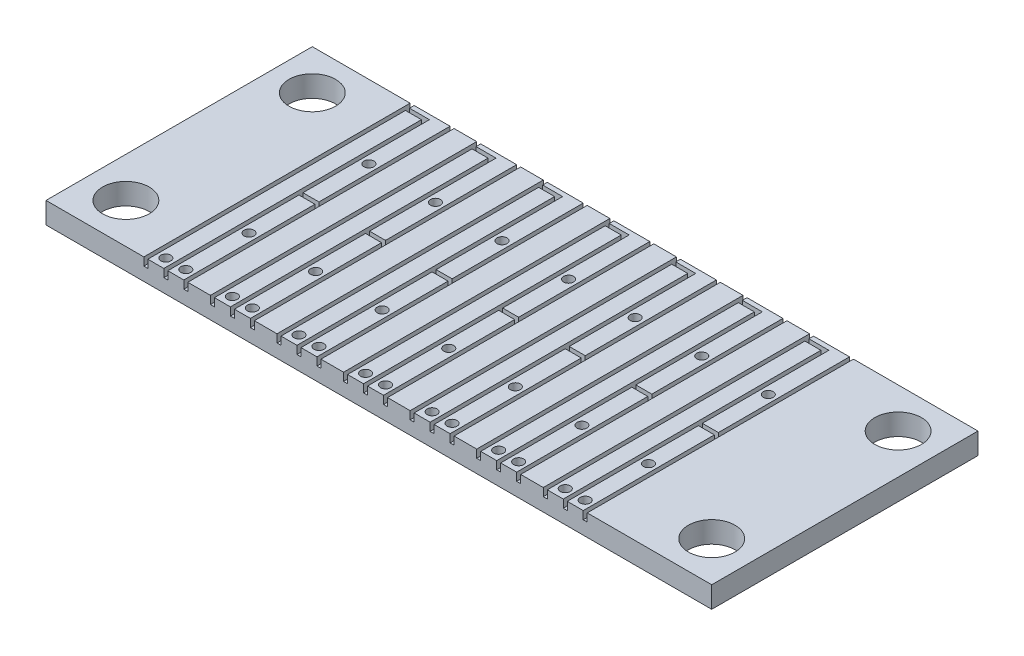
SolidWorks part; units mm, degrees
ref_plane "Front Plane" through (0, 0, 0) normal (0, 0, 1) x (1, 0, 0)
ref_plane "Top Plane" through (0, 0, 0) normal (0, 1, 0) x (1, 0, 0)
ref_plane "Right Plane" through (0, 0, 0) normal (1, 0, 0) x (0, 0, -1)
sketch "Sketch1" plane through (0, 0, 0) normal (0, 1, 0) x (1, 0, 0)
  line L1 (0, 0) -> (50, 0)
  line L2 (0, 0) -> (0, 20)
  line L3 (0, 20) -> (50, 20)
  line L4 (50, 0) -> (50, 20)
  circle A0 centre (3, 17) radius 1.75
  circle A1 centre (47, 3) radius 1.75
  circle A2 centre (3, 3) radius 1.75
  circle A3 centre (47, 17) radius 1.75
  dimension "D3" = 3.5
  dimension "D1" = 20
  dimension "D2" = 50
  dimension "D4" = 3
  dimension "D5" = 3
  dimension "D7" = 3
  dimension "D8" = 3
extrude "Boss-Extrude1" add sketch "Sketch1" along normal blind 1.6
sketch "Sketch2" plane through (0, 1.6, 0) normal (0, 1, 0) x (1, 0, 0)
  line L0 (50, 20) -> (0, 20) construction
  line L1 (7.5, 20) -> (10.5, 20)
  line L2 (7.5, 20) -> (7.5, 0)
  line L3 (7.5, 0) -> (10.5, 0)
  line L4 (10.5, 20) -> (10.5, 0)
  line L5 (0, 0) -> (50, 0) construction
  line L6 (0, 20) -> (0, 0) construction
  line L7 (9, 0) -> (9, 19.5)
  line L8 (9, 19.5) -> (7.5, 19.5)
  line L9 (10.5, 10) -> (9, 10)
  line L10 (9.15, 0) -> (9.15, 19.65)
  line L11 (9.15, 19.65) -> (7.5, 19.65)
  line L12 (8.85, 0) -> (8.85, 19.35)
  line L13 (8.85, 19.35) -> (7.5, 19.35)
  line L14 (7.35, 20) -> (7.35, 0)
  line L15 (7.65, 20) -> (7.65, 0)
  line L16 (10.35, 20) -> (10.35, 0)
  line L17 (10.65, 20) -> (10.65, 0)
  line L18 (10.5, 10.15) -> (9, 10.15)
  line L19 (10.5, 9.85) -> (9, 9.85)
  line L20 (7.35, 20) -> (7.65, 20)
  line L21 (10.35, 20) -> (10.65, 20)
  line L22 (7.5, 19.65) -> (7.5, 19.35)
  line L23 (9, 10.15) -> (9, 9.85)
  line L24 (10.5, 10.15) -> (10.5, 9.85)
  line L25 (7.35, 0) -> (7.65, 0)
  line L26 (8.85, 0) -> (9.15, 0)
  line L27 (10.35, 0) -> (10.65, 0)
  dimension "D1" = 7.5
  dimension "D2" = 3
  dimension "D3" = 0.5
  dimension "D4" = 0.15
  dimension "D5" = 0.15
  dimension "D6" = 0.15
  dimension "D7" = 0.15
  dimension "D8" = 0.15
  dimension "D9" = 0.15
  dimension "D10" = 0.15
  dimension "D11" = 0.15
sketch "Sketch3" plane through (0, 1.6, 0) normal (0, 1, 0) x (1, 0, 0)
  line L0 (7.5, 0) -> (10.5, 0) construction
  line L1 (10.5, 10) -> (9, 10) construction
  line L2 (9, 19.5) -> (7.5, 19.5) construction
  line L3 (9.75, 5.5) -> (9.75, 14.5) construction
  line L4 (8.25, 19.5) -> (8.25, 0.75) construction
  circle A0 centre (8.25, 0.75) radius 0.375
  circle A1 centre (9.75, 0.75) radius 0.375
  circle A2 centre (9.75, 5.5) radius 0.375
  circle A3 centre (9.75, 14.5) radius 0.375
  point P8 (8.25, 19.5)
  point P12 (9.75, 10)
  point P16 (9.75, 10)
  dimension "D1" = 0.75
  dimension "D3" = 9
  dimension "D2" = 0.75
extrude "Cut-Extrude1" cut sketch "Sketch3" against normal through all
extrude "Cut-Extrude2" cut sketch "Sketch2" against normal blind 0.6 contours L14 L25 L15 L20 | L12 L13 L22 L11 L10 L26 | L16 L27 L17 L21 | L19 L23 L18 L24
pattern_linear "LPattern1" count 7 spacing 5 along (1, 0, 0) of "Cut-Extrude1"
pattern_linear "LPattern2" count 7 spacing 5 along (1, 0, 0) of "Cut-Extrude2"
